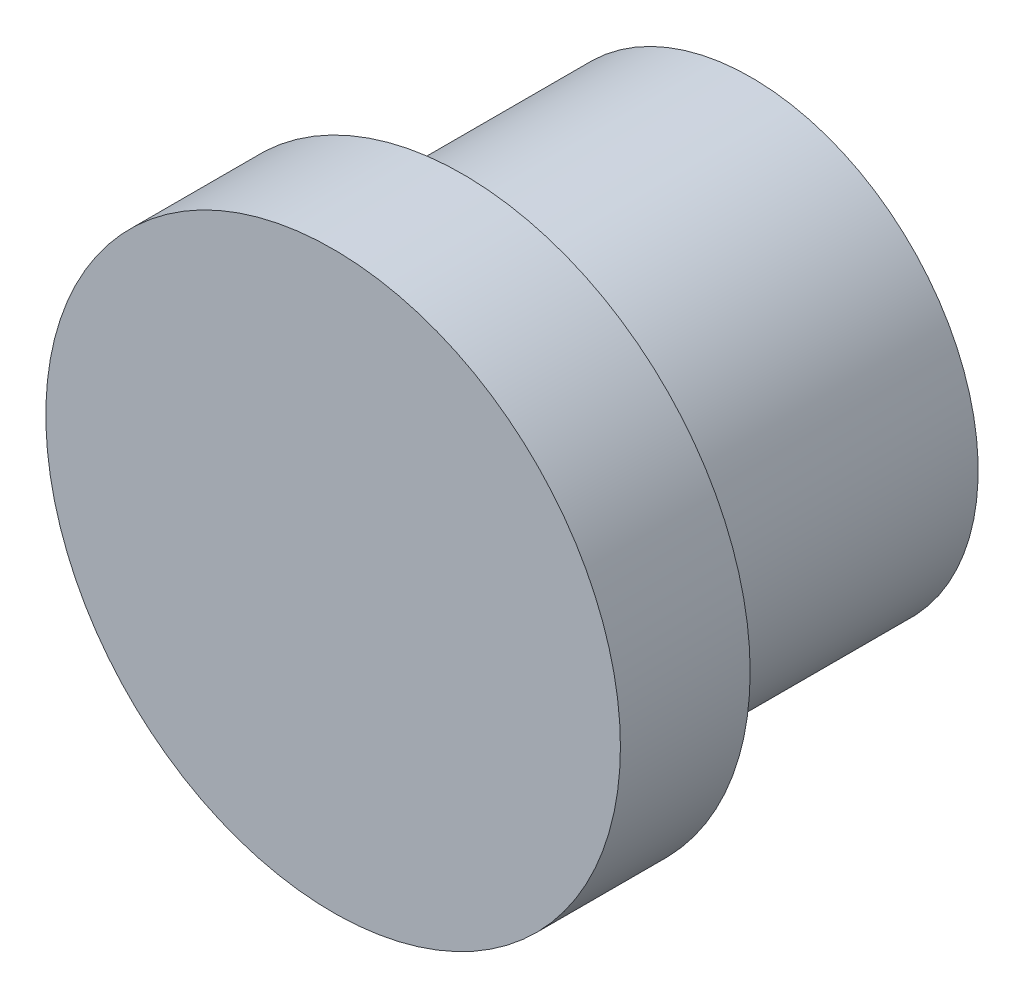
SolidWorks part; units mm, degrees
ref_plane "Front Plane" through (0, 0, 0) normal (0, 0, 1) x (1, 0, 0)
ref_plane "Top Plane" through (0, 0, 0) normal (0, 1, 0) x (1, 0, 0)
ref_plane "Right Plane" through (0, 0, 0) normal (1, 0, 0) x (0, 0, -1)
sketch "Sketch1" plane through (0, 0, 0) normal (0, 0, 1) x (1, 0, 0)
  circle A1 centre (0, 0) radius 9
extrude "Boss-Extrude1" add sketch "Sketch1" along normal blind 4.064
sketch "Sketch2" plane through (0, 0, 0) normal (0, 0, -1) x (-1, 0, 0)
  circle A0 centre (0, 0) radius 7.11
  point P3 (-26.0907, -0.8404)
extrude "Boss-Extrude2" add sketch "Sketch2" along normal blind 9.0329
